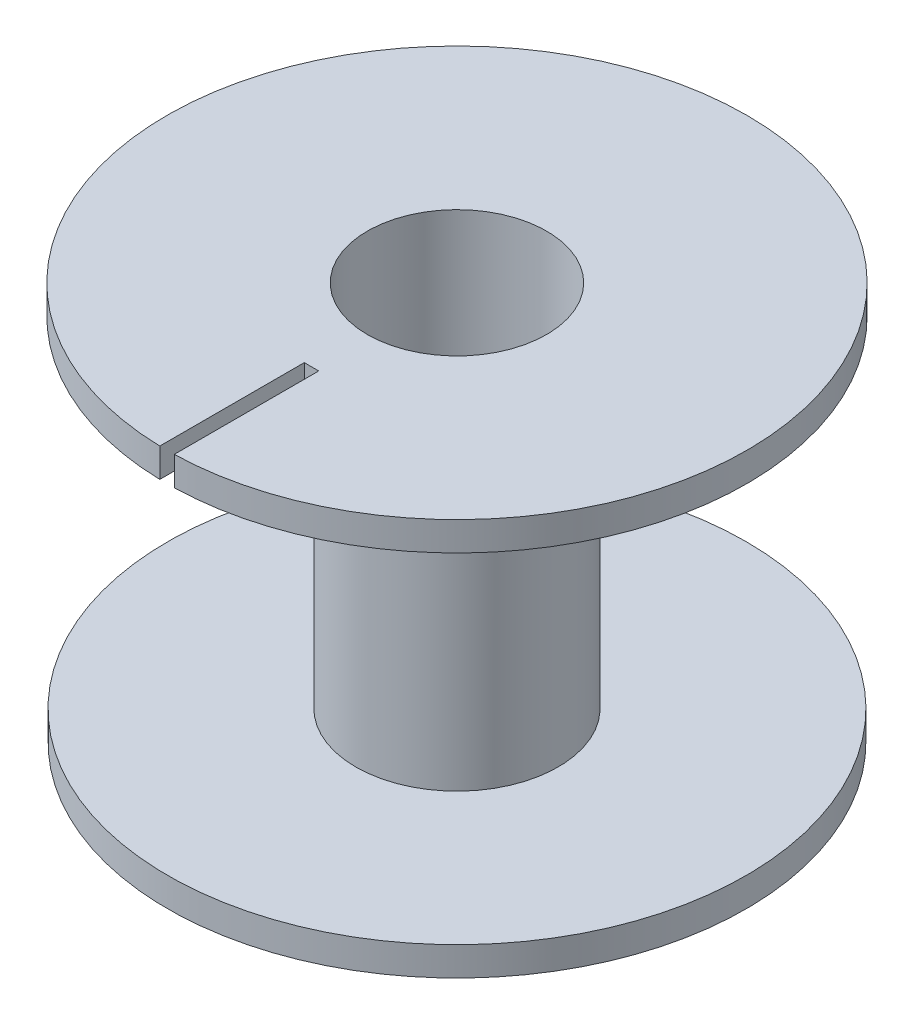
SolidWorks part; units mm, degrees
ref_plane "前视基准面" through (0, 0, 0) normal (0, 0, 1) x (1, 0, 0)
ref_plane "上视基准面" through (0, 0, 0) normal (0, 1, 0) x (1, 0, 0)
ref_plane "右视基准面" through (0, 0, 0) normal (1, 0, 0) x (0, 0, -1)
other "Configuration Table"
sketch "草图3" plane through (0, 0, 0) normal (0, 1, 0) x (1, 0, 0)
  line L3 (-0.5, -20.0522) -> (-0.5, -10.0584)
  line L5 (-0.5, -10.0584) -> (0.5, -10.0584)
  line L6 (0.5, -10.0584) -> (0.5, -20.0522)
  arc A0 (0.5, -20.0522) -> (-0.5, -20.0522) centre (0, 0) ccw
extrude "凸台-拉伸3" add sketch "草图3" along normal blind 2 contours A0 L3 L5 L6
sketch "草图5" plane through (0, 2, 0) normal (0, 1, 0) x (1, 0, 0)
  circle A0 centre (0, 0) radius 6.2
extrude "切除-拉伸2" cut sketch "草图5" against normal blind 2 contours A0
sketch "草图6" plane through (0, 0, 0) normal (0, -1, 0) x (-1, 0, 0)
  circle A0 centre (0, 0) radius 7
extrude "凸台-拉伸6" add sketch "草图6" along normal blind 23.5
sketch "草图7" plane through (0, 0, 0) normal (0, 1, 0) x (1, 0, 0)
  circle A0 centre (0, 0) radius 6.2
extrude "切除-拉伸3" cut sketch "草图7" against normal blind 23.5 contours A0
sketch "草图8" plane through (0, -23.5, 0) normal (0, -1, 0) x (1, 0, 0)
  circle A0 centre (0, 0) radius 20
extrude "凸台-拉伸7" add sketch "草图8" along normal blind 2
sketch "草图9" plane through (0, -25.5, 0) normal (0, -1, 0) x (1, 0, 0)
  circle A0 centre (0, 0) radius 6.2
extrude "切除-拉伸4" cut sketch "草图9" against normal blind 2
